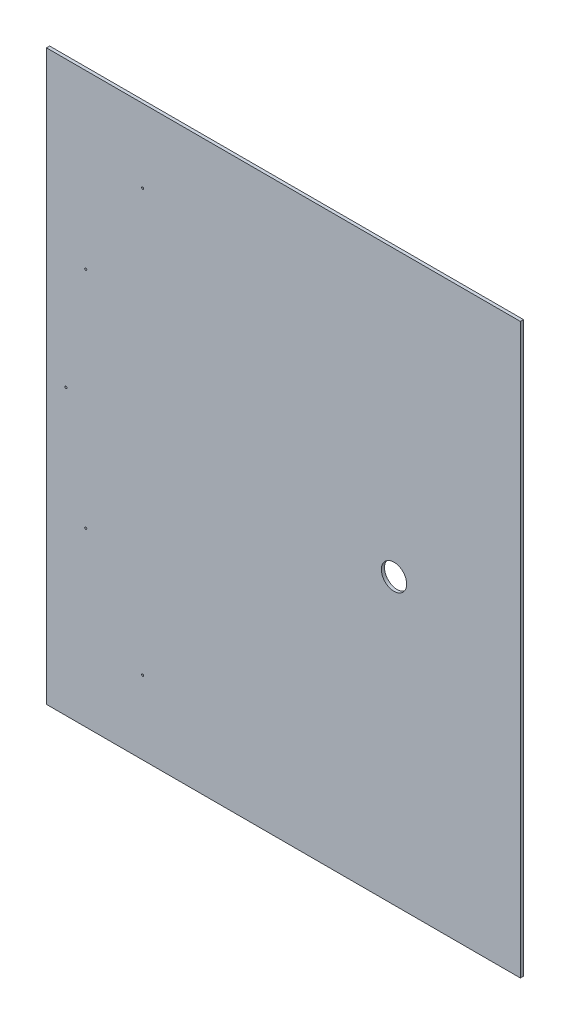
SolidWorks part; units mm, degrees
ref_plane "Plano frontal" through (0, 0, 0) normal (0, 0, 1) x (1, 0, 0)
ref_plane "Plano superior" through (0, 0, 0) normal (0, 1, 0) x (1, 0, 0)
ref_plane "Plano direito" through (0, 0, 0) normal (1, 0, 0) x (0, 0, -1)
sketch "Esboço1" plane through (0, 0, 0) normal (0, 0, 1) x (1, 0, 0)
  line L0 (-750, 0) -> (750, 0) construction
  line L1 (-750, -900) -> (750, -900)
  line L2 (-750, -900) -> (-750, 900)
  line L3 (-750, 900) -> (750, 900)
  line L4 (750, -900) -> (750, 900)
  line L5 (0, 900) -> (0, -900) construction
  dimension "D1" = 1800
  dimension "D2" = 1500
extrude "Ressalto-extrusão1" add sketch "Esboço1" along normal blind 10 contours L3 L4 L1 L2
sketch "Esboço2" plane through (0, 0, 10) normal (0, 0, 1) x (1, 0, 0)
  circle A0 centre (350, 0) radius 40
  dimension "D1" = 1100
  dimension "D3" = 80
extrude "Corte-extrusão1" cut sketch "Esboço2" against normal through all contours A0
hole_wizard "Furo com folga de M61" positions "Esboço3" profile "Esboço4" hole size "M6" standard "Ansi Metric"
sketch "Esboço3" plane through (350, 0, 16) normal (0, 0, 1) x (0, 1, 0)
  line L0 (0, 1001.785) -> (0, 1075) construction
  circle A2 centre (0, 0) radius 1038.3925 construction
  point P0 (0, 1038.3925)
  point P24 (355.1512, 975.7698)
  point P25 (667.4658, 795.4548)
  point P30 (-355.1512, 975.7698)
  point P31 (-667.4658, 795.4548)
sketch "Esboço4" plane through (-688.3925, 0, 16) normal (1, 0, 0) x (0, -1, 0)
  line L0 (0, 0) -> (0, 17.9818)
  line L1 (0, 17.9818) -> (3.3, 15.999)
  line L2 (3.3, 15.999) -> (3.3, 0)
  line L3 (3.3, 0) -> (0, 0)
  line L4 (0, 17.9818) -> (-3.3, 15.999) construction
  line L5 (0, -6.35) -> (0, 107.95) construction
  dimension "Hole Dia." = 6.6
  dimension "Hole Depth" = 15.999
  dimension "Drill Angle" = 118
